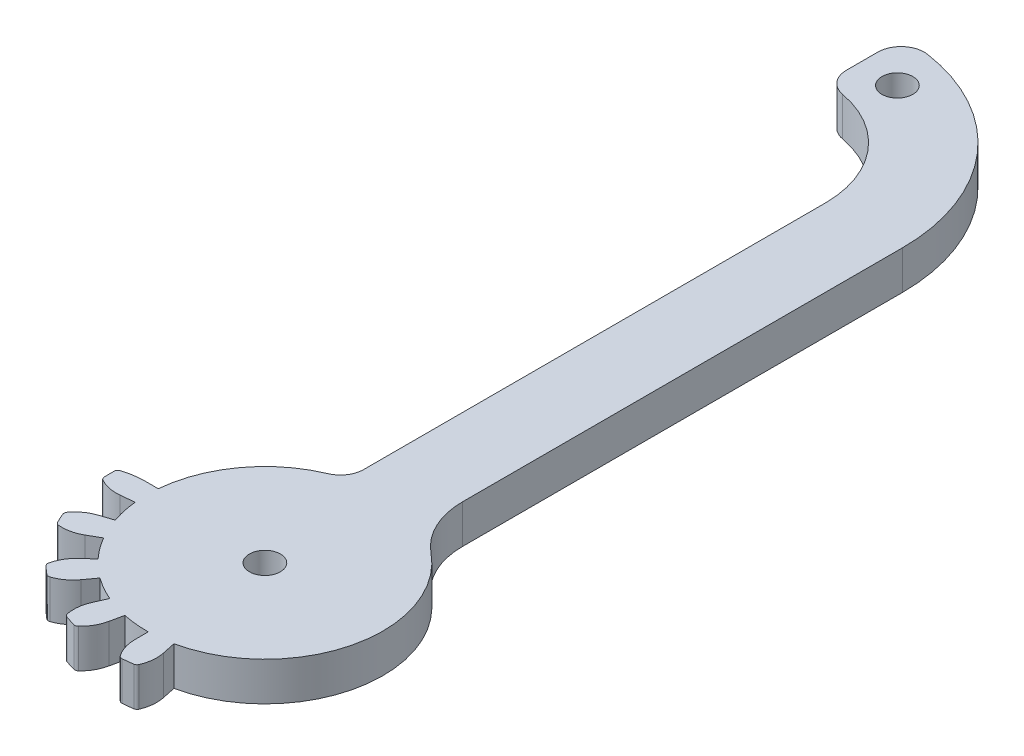
SolidWorks part; units mm, degrees
ref_plane "Front Plane" through (0, 0, 0) normal (0, 0, 1) x (1, 0, 0)
ref_plane "Top Plane" through (0, 0, 0) normal (0, 1, 0) x (1, 0, 0)
ref_plane "Right Plane" through (0, 0, 0) normal (1, 0, 0) x (0, 0, -1)
sketch "Sketch1" plane through (0, 0, 0) normal (0, 1, 0) x (1, 0, 0)
  line L1 (-15.1945, -20.4972) -> (-16.9345, -20.4972)
  line L3 (5.9355, -7.851) -> (5.9355, 54.5906)
  line L4 (-15.1765, -23.5035) -> (-16.9172, -23.6864)
  line L5 (-4.0645, -7.2006) -> (-4.0645, 54.5906)
  line L6 (-14.4556, -26.7984) -> (-16.1201, -27.3393)
  line L7 (-13.2161, -29.5385) -> (-14.7319, -30.4137)
  line L11 (-11.2173, -32.2554) -> (-12.5179, -33.4264)
  line L12 (-8.9704, -34.2544) -> (-9.9992, -35.6704)
  line L14 (-17.5645, 78.0906) -> (-17.5645, 68.0906)
  line L15 (-6.0394, -35.9234) -> (-6.7513, -37.5222)
  line L16 (-3.1737, -36.8357) -> (-3.5376, -38.5478)
  line L19 (0.1827, -37.1683) -> (0.1827, -38.9184)
  line L20 (3.1717, -36.8361) -> (3.5356, -38.5482)
  line L29 (13.215, -29.5403) -> (14.7309, -30.4154) [skipped]
  line L30 (8.9688, -34.2556) -> (9.9976, -35.6716) [skipped]
  arc A0 (-16.9345, -20.4972) -> (-19.991, -21.0444) centre (-16.9345, -29.3076) ccw
  arc A1 (-19.991, -21.0444) -> (-19.9823, -22.9566) centre (0, -21.9094) ccw
  arc A2 (-14.6018, -26.3429) -> (-14.4556, -26.7984) centre (0, -21.9094) ccw
  circle A3 centre (0, -21.9094) radius 2
  arc A4 (-16.9172, -23.6864) -> (-19.9823, -22.9566) centre (-17.4131, -18.9681) cw
  arc A5 (-15.1765, -23.5035) -> (-14.6018, -26.3429) centre (0, -21.9094) ccw
  arc A6 (-16.1201, -27.3393) -> (-18.6145, -29.2502) centre (-14.6449, -31.8484) ccw
  arc A7 (-18.6145, -29.2502) -> (-17.8288, -30.9936) centre (0, -21.9094) ccw
  arc A8 (-14.7319, -30.4137) -> (-17.8288, -30.9936) centre (-17.104, -26.305) cw
  arc A9 (-13.2161, -29.5385) -> (-11.5361, -31.8987) centre (0, -21.9094) ccw
  arc A10 (-11.5361, -31.8987) -> (-11.2173, -32.2554) centre (0, -21.9094) ccw
  arc A11 (-12.5179, -33.4264) -> (-14.0194, -36.1868) centre (-9.3362, -36.9457) ccw
  arc A12 (-14.0194, -36.1868) -> (-12.5925, -37.4598) centre (0, -21.9094) ccw
  arc A13 (-9.9992, -35.6704) -> (-12.5925, -37.4598) centre (-13.8375, -32.8818) cw
  arc A14 (-8.9704, -34.2544) -> (-6.4758, -35.7272) centre (0, -21.9094) ccw
  arc A15 (-6.4758, -35.7272) -> (-6.0394, -35.9234) centre (0, -21.9094) ccw
  arc A16 (-6.7513, -37.5222) -> (-7.0003, -40.6546) centre (-2.4132, -39.4432) ccw
  arc A17 (-7.0003, -40.6546) -> (-5.1789, -41.2373) centre (0, -21.9094) ccw
  arc A18 (-3.5376, -38.5478) -> (-5.1789, -41.2373) centre (-8.1783, -37.5614) cw
  arc A19 (-3.1737, -36.8357) -> (-0.2957, -37.1665) centre (0, -21.9094) ccw
  arc A20 (-0.2957, -37.1665) -> (0.1827, -37.1683) centre (0, -21.9094) ccw
  arc A21 (0.1827, -38.9184) -> (1.2293, -41.8813) centre (4.927, -38.9088) ccw
  arc A22 (1.2293, -41.8813) -> (3.1302, -41.6727) centre (0, -21.9094) ccw
  arc A23 (3.5356, -38.5482) -> (3.1302, -41.6727) centre (-1.105, -39.5346) cw
  arc A24 (3.1717, -36.8361) -> (5.9355, -7.851) centre (0, -21.9094) ccw
  circle A26 centre (-12.5645, 72.4021) radius 2
  arc A35 (-15.1945, -20.4972) -> (-4.0645, -7.2006) centre (0, -21.9094) cw
  arc A36 (-17.5645, 68.0906) -> (-4.0645, 54.5906) centre (-17.5645, 54.5906) cw
  arc A37 (-17.5645, 78.0906) -> (5.9355, 54.5906) centre (-17.5645, 54.5906) cw
  arc A40 (9.9976, -35.6716) -> (10.8981, -38.6909) centre (6.1594, -38.4603) cw [skipped]
  arc A41 (14.7309, -30.4154) -> (16.7815, -32.8075) centre (12.3587, -34.5241) cw [skipped]
  arc A42 (15.6646, -34.3596) -> (16.7815, -32.8075) centre (0, -21.9094) ccw [skipped]
  arc A43 (9.2463, -39.6546) -> (10.8981, -38.6909) centre (0, -21.9094) ccw [skipped]
  arc A44 (8.9688, -34.2556) -> (11.1404, -32.3382) centre (0, -21.9094) ccw [skipped]
  arc A45 (13.215, -29.5403) -> (14.419, -26.9054) centre (0, -21.9094) ccw [skipped]
  arc A46 (3.1717, -36.8361) -> (5.9355, -35.9678) centre (0, -21.9094) ccw [skipped]
  dimension "D1" = 10
  dimension "D4" = 7
extrude "Boss-Extrude3" add sketch "Sketch1" along normal blind 5 contours A37 L14 A36 L5 A35 L1 A0 A1 A4 L4 A5 A2 L6 A6 A7 A8 L7 A9 A10 L11 A11 A12 A13 L12 A14 A15 L15 A16 A17 A18 L16 A19 A20 L19 A21 A22 A23 L20 A24 L3 A3
fillet "Fillet11" radius 3 3 edges at (-17.5645, 2.5, -68.0906) (-17.5645, 2.5, -78.0906) (-4.0645, 2.5, 7.2006)
fillet "Fillet12" radius 10 1 edges at (5.9355, 2.5, 7.851)
fillet "Fillet13" radius 0.5 10 edges at (-19.991, 2.5, 21.0444) (-19.9823, 2.5, 22.9566) (-18.6145, 2.5, 29.2502) (-17.8288, 2.5, 30.9936) (-14.0194, 2.5, 36.1868) (-12.5925, 2.5, 37.4598) (-7.0003, 2.5, 40.6546) (-5.1789, 2.5, 41.2373) (1.2293, 2.5, 41.8813) (3.1302, 2.5, 41.6727)
